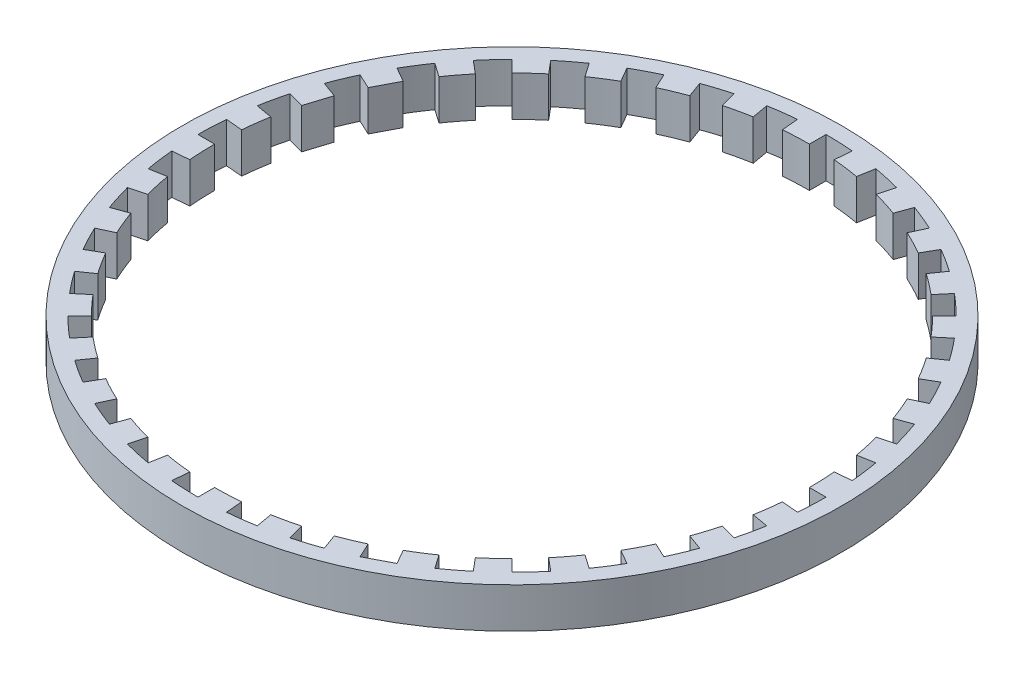
SolidWorks part; units mm, degrees
ref_plane "前视基准面" through (0, 0, 0) normal (0, 0, 1) x (1, 0, 0)
ref_plane "上视基准面" through (0, 0, 0) normal (0, 1, 0) x (1, 0, 0)
ref_plane "右视基准面" through (0, 0, 0) normal (1, 0, 0) x (0, 0, -1)
other "Configuration Table"
sketch "草图1" plane through (0, 0, 0) normal (0, 1, 0) x (1, 0, 0)
  line L0 (18.5, 0) -> (19.5346, 0)
  line L1 (18.4296, -1.6124) -> (19.4603, -1.7026)
  line L2 (18.2189, -3.2125) -> (19.2379, -3.3922)
  line L3 (17.8696, -4.7882) -> (18.869, -5.0559)
  line L4 (17.3843, -6.3274) -> (18.3565, -6.6812)
  line L5 (16.7667, -7.8184) -> (17.7044, -8.2557)
  line L6 (16.0215, -9.25) -> (16.9175, -9.7673)
  line L7 (15.1543, -10.6112) -> (16.0018, -11.2046)
  line L8 (14.1718, -11.8916) -> (14.9644, -12.5566)
  line L9 (13.0815, -13.0815) -> (13.8131, -13.8131)
  line L10 (11.8916, -14.1718) -> (12.5566, -14.9644)
  line L11 (10.6112, -15.1543) -> (11.2046, -16.0018)
  line L12 (9.25, -16.0215) -> (9.7673, -16.9175)
  line L13 (7.8184, -16.7667) -> (8.2557, -17.7044)
  line L14 (6.3274, -17.3843) -> (6.6812, -18.3565)
  line L15 (4.7882, -17.8696) -> (5.0559, -18.869)
  line L16 (3.2125, -18.2189) -> (3.3922, -19.2379)
  line L17 (1.6124, -18.4296) -> (1.7026, -19.4603)
  line L18 (0, -18.5) -> (0, -19.5346)
  line L19 (-1.6124, -18.4296) -> (-1.7026, -19.4603)
  line L20 (-3.2125, -18.2189) -> (-3.3922, -19.2379)
  line L21 (-4.7882, -17.8696) -> (-5.0559, -18.869)
  line L22 (-6.3274, -17.3843) -> (-6.6812, -18.3565)
  line L23 (-7.8184, -16.7667) -> (-8.2557, -17.7044)
  line L24 (-9.25, -16.0215) -> (-9.7673, -16.9175)
  line L25 (-10.6112, -15.1543) -> (-11.2046, -16.0018)
  line L27 (-13.0815, -13.0815) -> (-13.8131, -13.8131)
  line L28 (-14.1718, -11.8916) -> (-14.9644, -12.5566)
  line L29 (-15.1543, -10.6112) -> (-16.0018, -11.2046)
  line L30 (-16.0215, -9.25) -> (-16.9175, -9.7673)
  line L31 (-16.7667, -7.8184) -> (-17.7044, -8.2557)
  line L32 (-17.3843, -6.3274) -> (-18.3565, -6.6812)
  line L33 (-17.8696, -4.7882) -> (-18.869, -5.0559)
  line L34 (-18.2189, -3.2125) -> (-19.2379, -3.3922)
  line L35 (-18.4296, -1.6124) -> (-19.4603, -1.7026)
  line L36 (-18.5, 0) -> (-19.5346, 0)
  line L37 (-18.4296, 1.6124) -> (-19.4603, 1.7026)
  line L38 (-18.2189, 3.2125) -> (-19.2379, 3.3922)
  line L39 (-17.8696, 4.7882) -> (-18.869, 5.0559)
  line L40 (-17.3843, 6.3274) -> (-18.3565, 6.6812)
  line L41 (-16.7667, 7.8184) -> (-17.7044, 8.2557)
  line L42 (-16.0215, 9.25) -> (-16.9175, 9.7673)
  line L43 (-15.1543, 10.6112) -> (-16.0018, 11.2046)
  line L44 (-14.1718, 11.8916) -> (-14.9644, 12.5566)
  line L45 (-13.0815, 13.0815) -> (-13.8131, 13.8131)
  line L46 (-11.8916, 14.1718) -> (-12.5566, 14.9644)
  line L47 (-10.6112, 15.1543) -> (-11.2046, 16.0018)
  line L48 (-9.25, 16.0215) -> (-9.7673, 16.9175)
  line L49 (-7.8184, 16.7667) -> (-8.2557, 17.7044)
  line L50 (-6.3274, 17.3843) -> (-6.6812, 18.3565)
  line L51 (-4.7882, 17.8696) -> (-5.0559, 18.869)
  line L52 (-3.2125, 18.2189) -> (-3.3922, 19.2379)
  line L53 (-1.6124, 18.4296) -> (-1.7026, 19.4603)
  line L54 (0, 18.5) -> (0, 19.5346)
  line L55 (1.6124, 18.4296) -> (1.7026, 19.4603)
  line L56 (3.2125, 18.2189) -> (3.3922, 19.2379)
  line L57 (4.7882, 17.8696) -> (5.0559, 18.869)
  line L58 (6.3274, 17.3843) -> (6.6812, 18.3565)
  line L59 (7.8184, 16.7667) -> (8.2557, 17.7044)
  line L60 (9.25, 16.0215) -> (9.7673, 16.9175)
  line L61 (10.6112, 15.1543) -> (11.2046, 16.0018)
  line L63 (13.0815, 13.0815) -> (13.8131, 13.8131)
  line L64 (14.1718, 11.8916) -> (14.9644, 12.5566)
  line L65 (15.1543, 10.6112) -> (16.0018, 11.2046)
  line L66 (16.0215, 9.25) -> (16.9175, 9.7673)
  line L67 (16.7667, 7.8184) -> (17.7044, 8.2557)
  line L68 (17.3843, 6.3274) -> (18.3565, 6.6812)
  line L69 (17.8696, 4.7882) -> (18.869, 5.0559)
  line L70 (18.2189, 3.2125) -> (19.2379, 3.3922)
  line L71 (18.4296, 1.6124) -> (19.4603, 1.7026)
  line L72 (-11.8916, -14.1718) -> (-12.5566, -14.9644)
  line L73 (11.8916, 14.1718) -> (12.5566, 14.9644)
  line L74 (0, 0) -> (-4.504, -5.3676) [skipped]
  line L75 (-4.504, -5.3676) -> (0, 0) [skipped]
  line L76 (-17.8696, 4.7882) -> (-17.3843, 6.3274)
  line L77 (-16.7667, 7.8184) -> (-16.0215, 9.25)
  line L78 (8.2557, -17.7044) -> (9.7673, -16.9175)
  circle A0 centre (0, 0) radius 20.5
  arc A3 (17.4334, 0.8128) -> (17.481, 0.8144) centre (17.4334, 1.5252) ccw
  arc A4 (18.7772, 2.5649) -> (18.8253, 2.5708) centre (18.7114, 3.2993) ccw
  arc A5 (18.9875, 0.6897) -> (18.9828, 0.6897) centre (18.9828, 0) ccw
  arc A6 (17.4334, 2.2377) -> (17.3569, 2.2335) centre (17.4334, 1.5252) ccw
  arc A7 (-14.1718, 11.8916) -> (-15.1543, 10.6112) centre (0, 0) ccw
  arc A8 (-16.0018, 11.2046) -> (-16.9175, 9.7673) centre (0, 0) ccw
  arc A9 (-13.8131, 13.8131) -> (-14.9644, 12.5566) centre (0, 0) ccw
  arc A10 (-18.869, -5.0559) -> (-18.3565, -6.6812) centre (0, 0) ccw
  arc A11 (-18.2189, 3.2125) -> (-18.4296, 1.6124) centre (0, 0) ccw
  arc A12 (-11.8916, 14.1718) -> (-13.0815, 13.0815) centre (0, 0) ccw
  arc A13 (-9.25, 16.0215) -> (-10.6112, 15.1543) centre (0, 0) ccw
  arc A14 (-6.3274, 17.3843) -> (-7.8184, 16.7667) centre (0, 0) ccw
  arc A15 (0, 18.5) -> (-1.6124, 18.4296) centre (0, 0) ccw
  arc A16 (-3.2125, 18.2189) -> (-4.7882, 17.8696) centre (0, 0) ccw
  arc A17 (3.2125, 18.2189) -> (1.6124, 18.4296) centre (0, 0) ccw
  arc A18 (6.3274, 17.3843) -> (4.7882, 17.8696) centre (0, 0) ccw
  arc A19 (9.25, 16.0215) -> (7.8184, 16.7667) centre (0, 0) ccw
  arc A20 (11.8916, 14.1718) -> (10.6112, 15.1543) centre (0, 0) ccw
  arc A21 (14.1718, 11.8916) -> (13.0815, 13.0815) centre (0, 0) ccw
  arc A22 (16.0215, 9.25) -> (15.1543, 10.6112) centre (0, 0) ccw
  arc A23 (17.3843, 6.3274) -> (16.7667, 7.8184) centre (0, 0) ccw
  arc A24 (18.2189, 3.2125) -> (17.8696, 4.7882) centre (0, 0) ccw
  arc A25 (18.5, 0) -> (18.4296, 1.6124) centre (0, 0) ccw
  arc A26 (18.2189, -3.2125) -> (18.4296, -1.6124) centre (0, 0) ccw
  arc A27 (17.3843, -6.3274) -> (17.8696, -4.7882) centre (0, 0) ccw
  arc A28 (16.0215, -9.25) -> (16.7667, -7.8184) centre (0, 0) ccw
  arc A29 (14.1718, -11.8916) -> (15.1543, -10.6112) centre (0, 0) ccw
  arc A30 (11.8916, -14.1718) -> (13.0815, -13.0815) centre (0, 0) ccw
  arc A31 (9.25, -16.0215) -> (10.6112, -15.1543) centre (0, 0) ccw
  arc A32 (6.3274, -17.3843) -> (7.8184, -16.7667) centre (0, 0) ccw
  arc A33 (3.2125, -18.2189) -> (4.7882, -17.8696) centre (0, 0) ccw
  arc A34 (0, -18.5) -> (1.6124, -18.4296) centre (0, 0) ccw
  arc A35 (-3.2125, -18.2189) -> (-1.6124, -18.4296) centre (0, 0) ccw
  arc A36 (-6.3274, -17.3843) -> (-4.7882, -17.8696) centre (0, 0) ccw
  arc A37 (-9.25, -16.0215) -> (-7.8184, -16.7667) centre (0, 0) ccw
  arc A38 (-11.8916, -14.1718) -> (-10.6112, -15.1543) centre (0, 0) ccw
  arc A39 (-14.1718, -11.8916) -> (-13.0815, -13.0815) centre (0, 0) ccw
  arc A40 (-16.0215, -9.25) -> (-15.1543, -10.6112) centre (0, 0) ccw
  arc A41 (-17.3843, -6.3274) -> (-16.7667, -7.8184) centre (0, 0) ccw
  arc A42 (-18.2189, -3.2125) -> (-17.8696, -4.7882) centre (0, 0) ccw
  arc A43 (-18.5, 0) -> (-18.4296, -1.6124) centre (0, 0) ccw
  arc A44 (-19.4603, -1.7026) -> (-19.2379, -3.3922) centre (0, 0) ccw
  arc A45 (-19.4603, 1.7026) -> (-19.5346, 0) centre (0, 0) ccw
  arc A46 (-18.869, 5.0559) -> (-19.2379, 3.3922) centre (0, 0) ccw
  arc A47 (-17.7044, 8.2557) -> (-18.3565, 6.6812) centre (0, 0) ccw
  arc A48 (-11.2046, 16.0018) -> (-12.5566, 14.9644) centre (0, 0) ccw
  arc A49 (-8.2557, 17.7044) -> (-9.7673, 16.9175) centre (0, 0) ccw
  arc A50 (-5.0559, 18.869) -> (-6.6812, 18.3565) centre (0, 0) ccw
  arc A51 (-1.7026, 19.4603) -> (-3.3922, 19.2379) centre (0, 0) ccw
  arc A52 (1.7026, 19.4603) -> (0, 19.5346) centre (0, 0) ccw
  arc A53 (5.0559, 18.869) -> (3.3922, 19.2379) centre (0, 0) ccw
  arc A54 (8.2557, 17.7044) -> (6.6812, 18.3565) centre (0, 0) ccw
  arc A55 (11.2046, 16.0018) -> (9.7673, 16.9175) centre (0, 0) ccw
  arc A56 (13.8131, 13.8131) -> (12.5566, 14.9644) centre (0, 0) ccw
  arc A57 (17.7044, 8.2557) -> (16.9175, 9.7673) centre (0, 0) ccw
  arc A58 (18.869, 5.0559) -> (18.3565, 6.6812) centre (0, 0) ccw
  arc A59 (19.4603, -1.7026) -> (19.5346, 0) centre (0, 0) ccw
  arc A60 (18.869, -5.0559) -> (19.2379, -3.3922) centre (0, 0) ccw
  arc A61 (17.7044, -8.2557) -> (18.3565, -6.6812) centre (0, 0) ccw
  arc A62 (16.0018, -11.2046) -> (16.9175, -9.7673) centre (0, 0) ccw
  arc A63 (13.8131, -13.8131) -> (14.9644, -12.5566) centre (0, 0) ccw
  arc A64 (11.2046, -16.0018) -> (12.5566, -14.9644) centre (0, 0) ccw
  arc A65 (5.0559, -18.869) -> (6.6812, -18.3565) centre (0, 0) ccw
  arc A66 (1.7026, -19.4603) -> (3.3922, -19.2379) centre (0, 0) ccw
  arc A67 (-1.7026, -19.4603) -> (0, -19.5346) centre (0, 0) ccw
  arc A68 (-5.0559, -18.869) -> (-3.3922, -19.2379) centre (0, 0) ccw
  arc A69 (-8.2557, -17.7044) -> (-6.6812, -18.3565) centre (0, 0) ccw
  arc A70 (-11.2046, -16.0018) -> (-9.7673, -16.9175) centre (0, 0) ccw
  arc A71 (-13.8131, -13.8131) -> (-12.5566, -14.9644) centre (0, 0) ccw
  arc A72 (-16.0018, -11.2046) -> (-14.9644, -12.5566) centre (0, 0) ccw
  arc A73 (-17.7044, -8.2557) -> (-16.9175, -9.7673) centre (0, 0) ccw
  arc A74 (19.4603, 1.7026) -> (19.2379, 3.3922) centre (0, 0) ccw
  arc A75 (16.0018, 11.2046) -> (14.9644, 12.5566) centre (0, 0) ccw
  point P89 (0, 0)
  dimension "D1" = 72
extrude "凸台-拉伸1" add sketch "草图1" along normal blind 2.5
